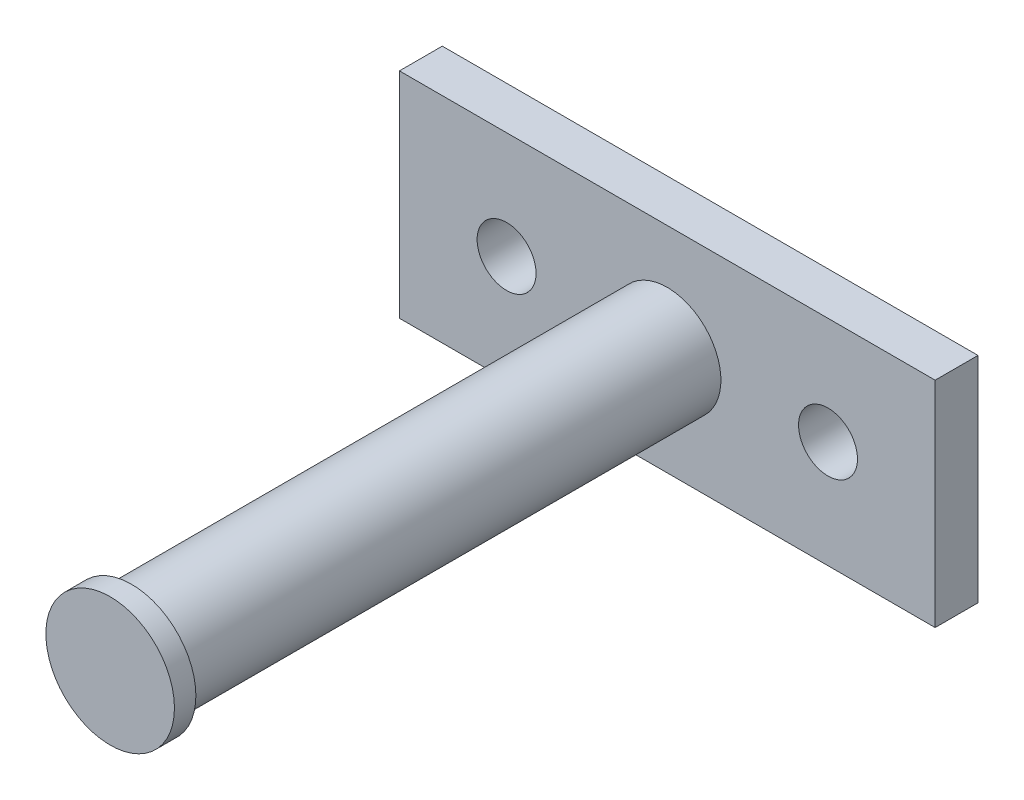
SolidWorks part; units mm, degrees
material "6063-T5"
ref_plane "Front Plane" through (0, 0, 0) normal (0, 0, 1) x (1, 0, 0)
ref_plane "Top Plane" through (0, 0, 0) normal (0, 1, 0) x (1, 0, 0)
ref_plane "Right Plane" through (0, 0, 0) normal (1, 0, 0) x (0, 0, -1)
sketch "Sketch1" plane through (0, 0, 0) normal (0, 0, 1) x (1, 0, 0)
  line L1 (-25, -10) -> (25, -10)
  line L2 (-25, -10) -> (-25, 10)
  line L3 (-25, 10) -> (25, 10)
  line L4 (25, -10) -> (25, 10)
  line L5 (-25, -10) -> (25, 10) construction
  line L6 (-25, 10) -> (25, -10) construction
  circle A1 centre (15, 0) radius 2.75
  circle A2 centre (-15, 0) radius 2.75
  point P0 (0, 0)
  dimension "D4" = 5.5
  dimension "D1" = 20
  dimension "D2" = 50
  dimension "D5" = 10
  dimension "D6" = 10
extrude "Boss-Extrude1" add sketch "Sketch1" against normal blind 4
sketch "Sketch2" plane through (0, 0, 0) normal (0, 0, 1) x (1, 0, 0)
  circle A0 centre (0, 0) radius 5
  dimension "D1" = 10
extrude "Boss-Extrude2" add sketch "Sketch2" along normal blind 50
sketch "Sketch3" plane through (0, 0, 50) normal (0, 0, 1) x (1, 0, 0)
  circle A0 centre (0, 0) radius 6
  dimension "D1" = 12
extrude "Boss-Extrude3" add sketch "Sketch3" along normal blind 2
